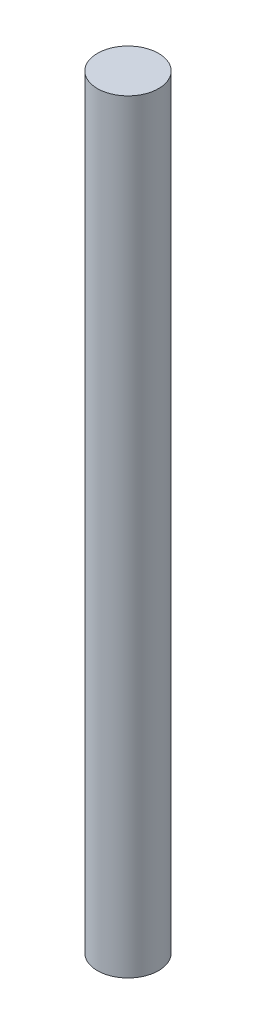
SolidWorks part; units mm, degrees
ref_plane "Front Plane" through (0, 0, 0) normal (0, 0, 1) x (1, 0, 0)
ref_plane "Top Plane" through (0, 0, 0) normal (0, 1, 0) x (1, 0, 0)
ref_plane "Right Plane" through (0, 0, 0) normal (1, 0, 0) x (0, 0, -1)
sketch "Sketch1" plane through (0, 0, 0) normal (0, 1, 0) x (1, 0, 0)
  circle A0 centre (0, 0) radius 4
  dimension "D1" = 8
extrude "Boss-Extrude1" add sketch "Sketch1" along normal blind 100
